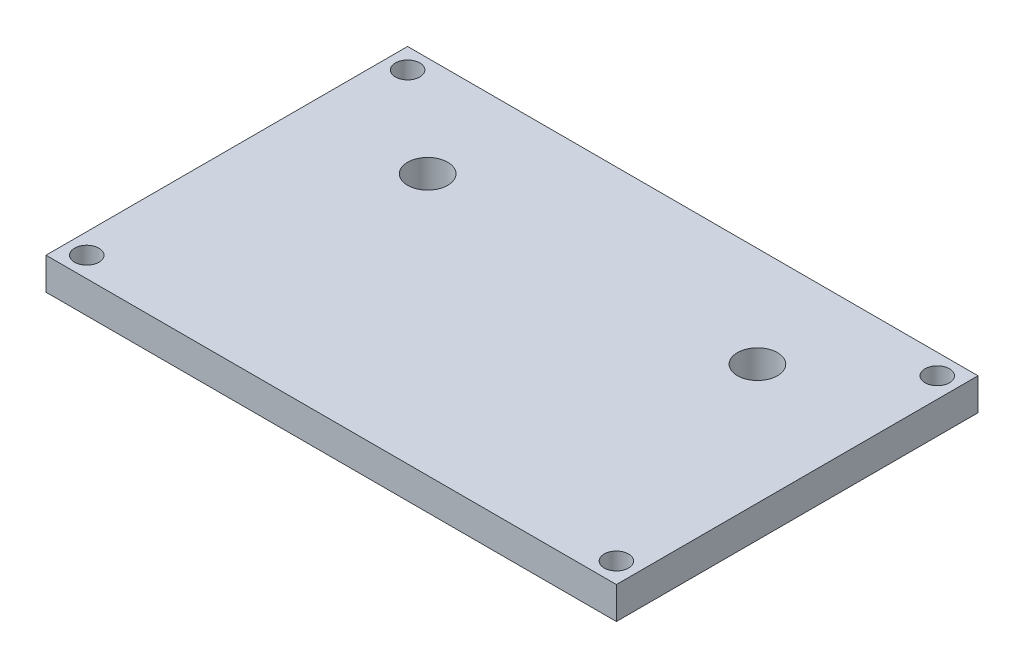
SolidWorks part; units mm, degrees
ref_plane "Front" through (0, 0, 0) normal (0, 0, 1) x (1, 0, 0)
ref_plane "Top" through (0, 0, 0) normal (0, 1, 0) x (1, 0, 0)
ref_plane "Right" through (0, 0, 0) normal (1, 0, 0) x (0, 0, -1)
sketch "Sketch1" plane through (0, 0, 0) normal (0, 1, 0) x (1, 0, 0)
  line L0 (0, 15.8303) -> (0, -14.7333) construction
  line L1 (-35.56, 22.5425) -> (35.56, 22.5425)
  line L2 (-35.56, 22.5425) -> (-35.56, -22.5425)
  line L3 (-35.56, -22.5425) -> (35.56, -22.5425)
  line L4 (35.56, 22.5425) -> (35.56, -22.5425)
  line L5 (-35.56, 22.5425) -> (35.56, -22.5425) construction
  line L6 (-35.56, -22.5425) -> (35.56, 22.5425) construction
  line L7 (-17.413, 0) -> (18.9134, 0) construction
  circle A0 centre (-33.02, 20.0025) radius 1.524
  circle A1 centre (33.02, 20.0025) radius 1.524
  circle A2 centre (33.02, -20.0025) radius 1.524
  circle A3 centre (-33.02, -20.0025) radius 1.524
  circle A4 centre (-20.56, 10.0425) radius 2.5
  circle A5 centre (20.56, 10.0425) radius 2.5
  point P0 (0, 0)
  dimension "D3" = 3.048
  dimension "D6" = 12.5
  dimension "D1" = 45.085
  dimension "D2" = 71.12
  dimension "D4" = 2.54
  dimension "D5" = 2.54
  dimension "D7" = 15
extrude "Boss-Extrude1" add sketch "Sketch1" along normal blind 4
